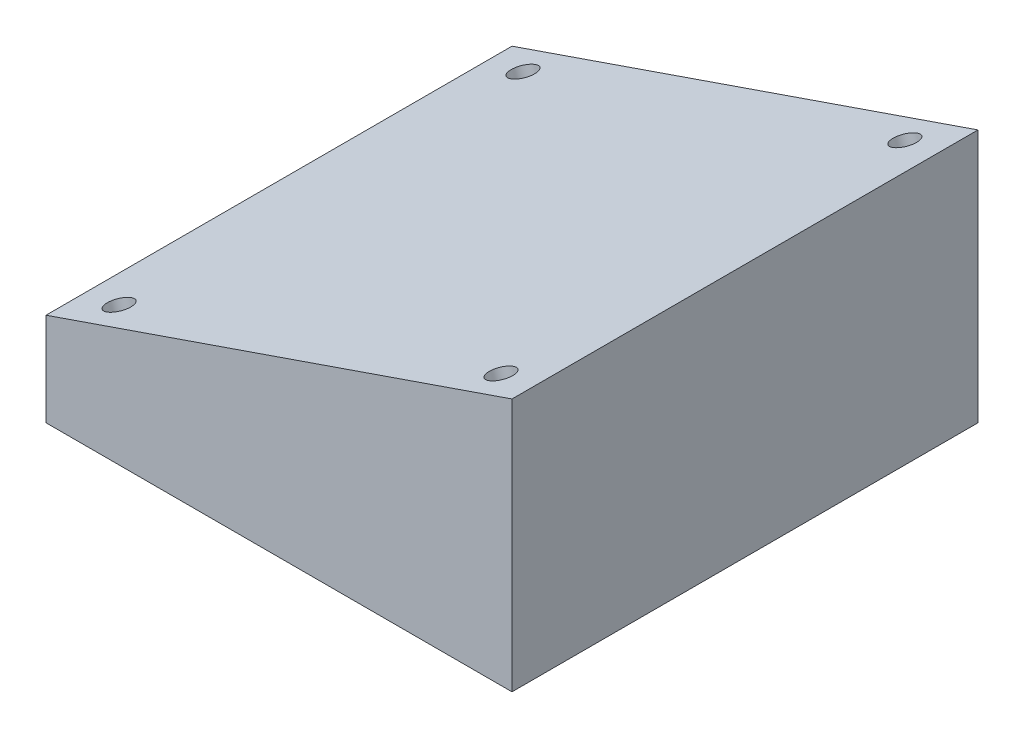
SolidWorks part; units mm, degrees
material "7075-T6 (SN)"
ref_plane "Plano frontal" through (0, 0, 0) normal (0, 0, 1) x (1, 0, 0)
ref_plane "Plano superior" through (0, 0, 0) normal (0, 1, 0) x (1, 0, 0)
ref_plane "Plano direito" through (0, 0, 0) normal (1, 0, 0) x (0, 0, -1)
sketch "Esboço1" plane through (0, 0, 0) normal (0, 1, 0) x (1, 0, 0)
  line L1 (-150, -150) -> (150, -150)
  line L2 (-150, -150) -> (-150, 150)
  line L3 (-150, 150) -> (150, 150)
  line L4 (150, -150) -> (150, 150)
  line L5 (-150, -150) -> (150, 150) construction
  line L6 (-150, 150) -> (150, -150) construction
  point P0 (0, 0)
  dimension "D1" = 300
extrude "Ressalto-extrusão1" add sketch "Esboço1" along normal blind 60
hole_wizard "Furo roscado de M14x2.01" [suppressed] positions "Esboço3" profile "Esboço2" tap size "M14x2.0" standard "Ansi Metric"
sketch "Esboço3" plane through (0, 0, 0) normal (0, -1, 0) x (-1, 0, 0)
  line L0 (0, 0) -> (0, -100) construction
  line L1 (100, -100) -> (-100, -100) construction
  line L2 (0, 0) -> (-100, 0) construction
  line L3 (-100, -100) -> (-100, 100) construction
  point P0 (47.5, -58)
  point P18 (-47.5, -58)
  point P21 (-47.5, 58)
  point P22 (47.5, 58)
  dimension "D1" = 95
  dimension "D2" = 116
sketch "Esboço2" plane through (-47.5, 0, 58) normal (1, 0, 0) x (0, 0, -1)
  line L0 (0, 0) -> (0, 13.6052)
  line L1 (0, 13.6052) -> (6, 10)
  line L2 (6, 10) -> (6, 0)
  line L5 (6, 0) -> (0, 0)
  line L10 (0, 13.6052) -> (-6, 10) construction
  line L11 (0, -6.35) -> (0, 107.95) construction
  dimension "Tap Drill Dia." = 12
  dimension "Tap Drill Depth" = 10
  dimension "Drill Angle" = 118
cosmetic thread "Rosca de furo1" [suppressed] parameters "D1"=10, "D2"=14
cosmetic thread "Rosca de furo2" [suppressed] parameters "D1"=10, "D2"=14
cosmetic thread "Rosca de furo3" [suppressed] parameters "D1"=10, "D2"=14
cosmetic thread "Rosca de furo4" [suppressed] parameters "D1"=10, "D2"=14
hole_wizard "Furo roscado de M10x1.51" [suppressed] positions "Esboço7" profile "Esboço6" tap size "M10x1.5" standard "Ansi Metric"
sketch "Esboço7" plane through (0, 20, 0) normal (0, 1, 0) x (1, 0, 0)
  line L0 (0, 0) -> (0, 100) construction
  line L1 (100, 100) -> (-100, 100) construction
  line L2 (0, 0) -> (100, 0) construction
  line L3 (100, -100) -> (100, 100) construction
  point P0 (-86.975, 86.975)
  point P13 (86.975, 86.975)
  point P14 (86.975, -86.975)
  point P15 (-86.975, -86.975)
  dimension "D1" = 173.95
  dimension "D2" = 173.95
sketch "Esboço6" plane through (-86.975, 20, -86.975) normal (1, 0, 0) x (0, 0, 1)
  line L0 (0, 0) -> (0, 12.5537)
  line L1 (0, 12.5537) -> (4.25, 10)
  line L2 (4.25, 10) -> (4.25, 0)
  line L5 (4.25, 0) -> (0, 0)
  line L10 (0, 12.5537) -> (-4.25, 10) construction
  line L11 (0, -6.35) -> (0, 107.95) construction
  dimension "Tap Drill Dia." = 8.5
  dimension "Tap Drill Depth" = 10
  dimension "Drill Angle" = 118
cosmetic thread "Rosca de furo5" [suppressed] parameters "D1"=10, "D2"=10
cosmetic thread "Rosca de furo6" [suppressed] parameters "D1"=10, "D2"=10
cosmetic thread "Rosca de furo7" [suppressed] parameters "D1"=10, "D2"=10
cosmetic thread "Rosca de furo8" [suppressed] parameters "D1"=10, "D2"=10
hole_wizard "Furo roscado de M16x2.01" positions "Esboço9" profile "Esboço8" tap size "M16x2.0" standard "Ansi Metric"
sketch "Esboço9" plane through (0, 0, 0) normal (0, -1, 0) x (-1, 0, 0)
  line L0 (0, 0) -> (0, -150) construction
  line L1 (150, -150) -> (-150, -150) construction
  line L2 (0, 0) -> (-150, 0) construction
  line L3 (-150, -150) -> (-150, 150) construction
  point P0 (55, -71)
  point P13 (-55, -71)
  point P15 (-55, 71)
  point P16 (55, 71)
  dimension "D1" = 110
  dimension "D2" = 142
sketch "Esboço8" plane through (-55, 0, 71) normal (1, 0, 0) x (0, 0, -1)
  line L0 (0, 0) -> (0, 14.206)
  line L1 (0, 14.206) -> (7, 10)
  line L2 (7, 10) -> (7, 0)
  line L5 (7, 0) -> (0, 0)
  line L10 (0, 14.206) -> (-7, 10) construction
  line L11 (0, -6.35) -> (0, 107.95) construction
  dimension "Tap Drill Dia." = 14
  dimension "Tap Drill Depth" = 10
  dimension "Drill Angle" = 118
cosmetic thread "Rosca de furo9" parameters "D1"=8, "D2"=16
cosmetic thread "Rosca de furo10" parameters "D1"=8, "D2"=16
cosmetic thread "Rosca de furo11" parameters "D1"=8, "D2"=16
cosmetic thread "Rosca de furo12" parameters "D1"=8, "D2"=16
sketch "Esboço12" plane through (0, 0, 0) normal (0, 0, 1) x (1, 0, 0)
  line L0 (-150, 60) -> (150, 163.2983)
  line L1 (150, 163.2983) -> (150, 60)
  line L2 (-150, 60) -> (150, 60) construction
  line L3 (-150, 60) -> (150, 60)
  dimension "D1" = 19
extrude "Ressalto-extrusão2" add sketch "Esboço12" along normal up to surface and the other way up to surface up to face at (0, 30, 150) other way up to face at (0, 30, -150)
hole_wizard "Furo roscado de M18x2.01" positions "Esboço14" profile "Esboço13" tap size "M18x2.0" standard "Ansi Metric"
sketch "Esboço14" plane through (-34.369, 99.8149, 0) normal (-0.3256, 0.9455, 0) x (0.9455, 0.3256, 0)
  line L0 (36.3494, 150) -> (36.3494, -150) construction
  line L1 (-122.2937, 150) -> (194.9925, 150) construction
  line L2 (-122.2937, -150) -> (194.9925, -150) construction
  line L4 (-122.2937, 0) -> (194.9925, 0) construction
  line L5 (-122.2937, 150) -> (-122.2937, -150) construction
  line L6 (194.9925, -150) -> (194.9925, 150) construction
  point P0 (-93.6506, 130)
  point P26 (166.3494, 130)
  point P29 (166.3494, -130)
  point P30 (-93.6506, -130)
  dimension "D1" = 130
  dimension "D2" = 130
sketch "Esboço13" plane through (-122.9174, 69.3253, -130) normal (0, 0, 1) x (-0.9455, -0.3256, 0)
  line L0 (0, 0) -> (0, 22.8069)
  line L1 (0, 22.8069) -> (8, 18)
  line L2 (8, 18) -> (8, 0)
  line L5 (8, 0) -> (0, 0)
  line L10 (0, 22.8069) -> (-8, 18) construction
  line L11 (0, -6.35) -> (0, 107.95) construction
  dimension "Tap Drill Dia." = 16
  dimension "Tap Drill Depth" = 18
  dimension "Drill Angle" = 118
cosmetic thread "Rosca de furo13" parameters "D1"=8, "D2"=18
cosmetic thread "Rosca de furo14" parameters "D1"=8, "D2"=18
cosmetic thread "Rosca de furo15" parameters "D1"=8, "D2"=18
cosmetic thread "Rosca de furo16" parameters "D1"=8, "D2"=18
equation "\"D2@Esboço7\"=\"D1@Esboço7\""
